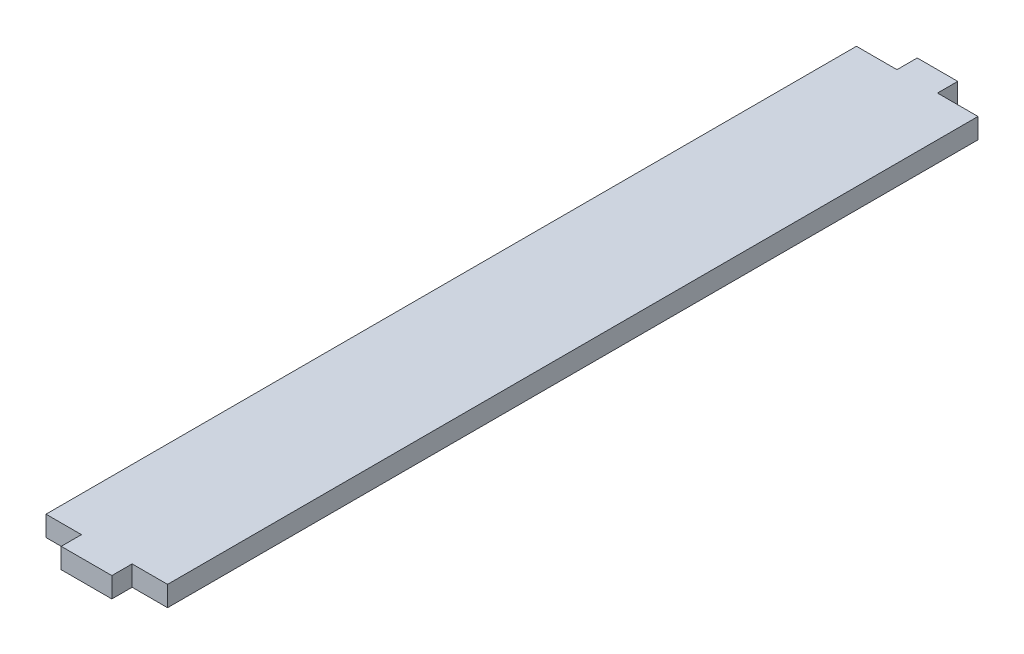
SolidWorks part; units mm, degrees
ref_plane "Front Plane" through (0, 0, 0) normal (0, 0, 1) x (1, 0, 0)
ref_plane "Top Plane" through (0, 0, 0) normal (0, 1, 0) x (1, 0, 0)
ref_plane "Right Plane" through (0, 0, 0) normal (1, 0, 0) x (0, 0, -1)
sketch "Sketch1" plane through (0, 0, 0) normal (0, 1, 0) x (1, 0, 0)
  line L0 (76.9168, -36.5625) -> (89.4168, -36.5625)
  line L1 (68.1668, 168.4375) -> (98.1668, 168.4375)
  line L2 (68.1668, 168.4375) -> (68.1668, -31.5625)
  line L3 (68.1668, -31.5625) -> (98.1668, -31.5625)
  line L4 (98.1668, 168.4375) -> (98.1668, -31.5625)
  line L5 (78.1668, 163.4375) -> (88.1668, 163.4375)
  line L6 (78.1668, 163.4375) -> (78.1668, 173.4375)
  line L7 (78.1668, 173.4375) -> (88.1668, 173.4375)
  line L8 (88.1668, 163.4375) -> (88.1668, 173.4375)
  line L9 (78.1668, 163.4375) -> (88.1668, 173.4375) construction
  line L10 (78.1668, 173.4375) -> (88.1668, 163.4375) construction
  line L11 (76.9168, -36.5625) -> (76.9168, -26.5625)
  line L12 (76.9168, -26.5625) -> (89.4168, -26.5625)
  line L13 (89.4168, -36.5625) -> (89.4168, -26.5625)
  line L14 (76.9168, -36.5625) -> (89.4168, -26.5625) construction
  line L15 (76.9168, -26.5625) -> (89.4168, -36.5625) construction
  point P4 (83.1668, 168.4375)
  point P9 (83.1668, -31.5625)
  dimension "D1" = 200
  dimension "D2" = 30
  dimension "D3" = 10
  dimension "D4" = 5
  dimension "D5" = 5
extrude "Boss-Extrude1" add sketch "Sketch1" along normal blind 5 contours L13 L3 L4 L1 L8 L5 L6 L2 L11 L12
equation "\"mat\"=\"mat@V1.assembly\""
equation "\"D4@Sketch1\"=\"mat\""
equation "\"D1@Boss-Extrude1\"=\"mat\""
equation "\"D5@Sketch1\" = \"mat\""
